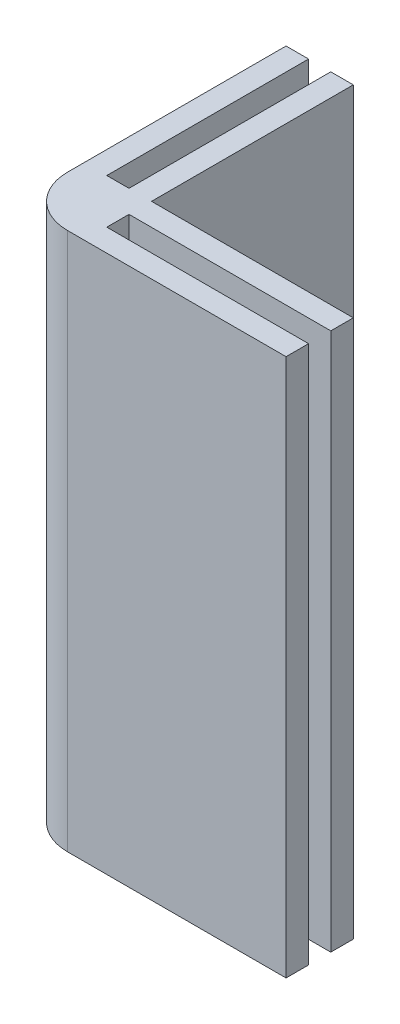
SolidWorks part; units mm, degrees
ref_plane "Front Plane" through (0, 0, 0) normal (0, 0, 1) x (1, 0, 0)
ref_plane "Top Plane" through (0, 0, 0) normal (0, 1, 0) x (1, 0, 0)
ref_plane "Right Plane" through (0, 0, 0) normal (1, 0, 0) x (0, 0, -1)
sketch "Sketch1" plane through (0, 0, 0) normal (0, 1, 0) x (1, 0, 0)
  line L0 (40, 3.35) -> (10, 3.35)
  line L1 (0, 0) -> (40, 0)
  line L2 (0, 0) -> (0, 40)
  line L3 (0, 40) -> (3.35, 40)
  line L4 (10, 3.35) -> (10, 6.65)
  line L5 (0, 0) -> (40, 0)
  line L6 (0, 0) -> (0, 40)
  line L7 (3.35, 10) -> (6.65, 10)
  line L8 (40, 0) -> (40, 3.35)
  line L9 (40, 6.65) -> (10, 6.65)
  line L10 (3.35, 10) -> (3.35, 40)
  line L11 (6.65, 40) -> (6.65, 10)
  line L12 (10, 10) -> (40, 10)
  line L13 (10, 10) -> (10, 40)
  line L14 (6.65, 40) -> (10, 40)
  line L15 (40, 6.65) -> (40, 10)
  dimension "D1" = 40
  dimension "D2" = 40
  dimension "D3" = 10
  dimension "D4" = 10
  dimension "D5" = 3.3
  dimension "D6" = 3.35
  dimension "D7" = 3.35
  dimension "D8" = 3.3
extrude "Boss-Extrude1" add sketch "Sketch1" along normal blind 80 contours L9 L15 L12 L13 L14 L11 L7 L10 L3 L2 L1 L8 L0 L4
fillet "Fillet1" radius 7.5 1 edges at (0, 40, 0)
